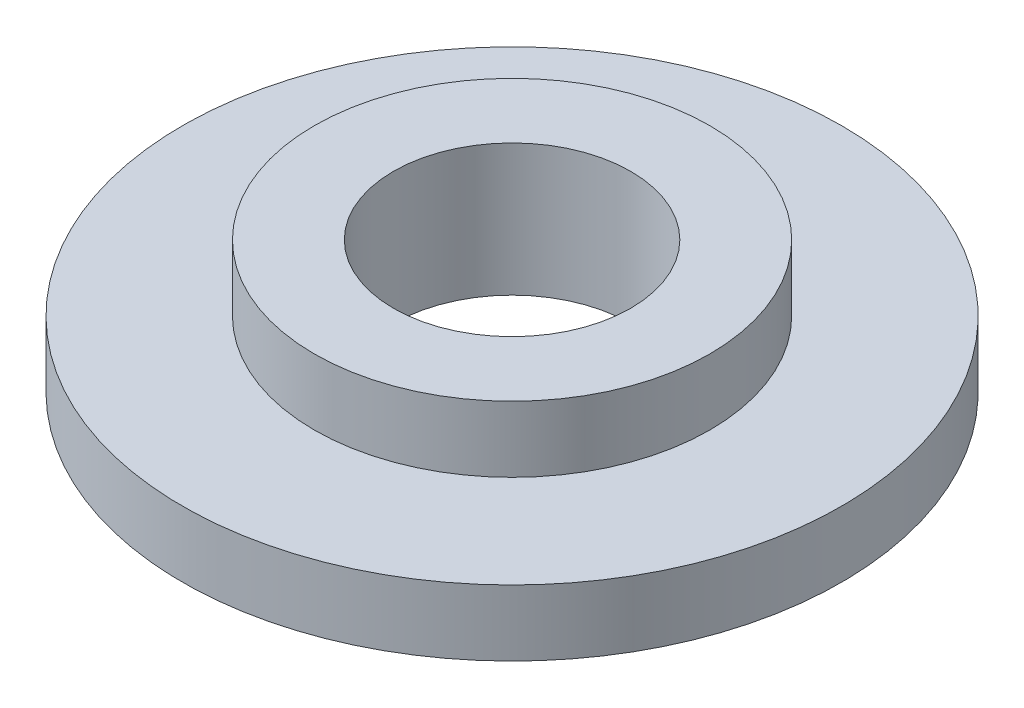
SolidWorks part; units mm, degrees
ref_plane "Front Plane" through (0, 0, 0) normal (0, 0, 1) x (1, 0, 0)
ref_plane "Top Plane" through (0, 0, 0) normal (0, 1, 0) x (1, 0, 0)
ref_plane "Right Plane" through (0, 0, 0) normal (1, 0, 0) x (0, 0, -1)
sketch "Sketch1" plane through (0, 0, 0) normal (0, 1, 0) x (1, 0, 0)
  circle A0 centre (0, 0) radius 1.8
  circle A1 centre (0, 0) radius 3
extrude "Boss-Extrude1" add sketch "Sketch1" along normal blind 1
sketch "Sketch2" plane through (0, 0, 0) normal (0, -1, 0) x (1, 0, 0)
  circle A0 centre (0, 0) radius 1.8
  circle A1 centre (0, 0) radius 5
extrude "Boss-Extrude2" add sketch "Sketch2" along normal blind 1
